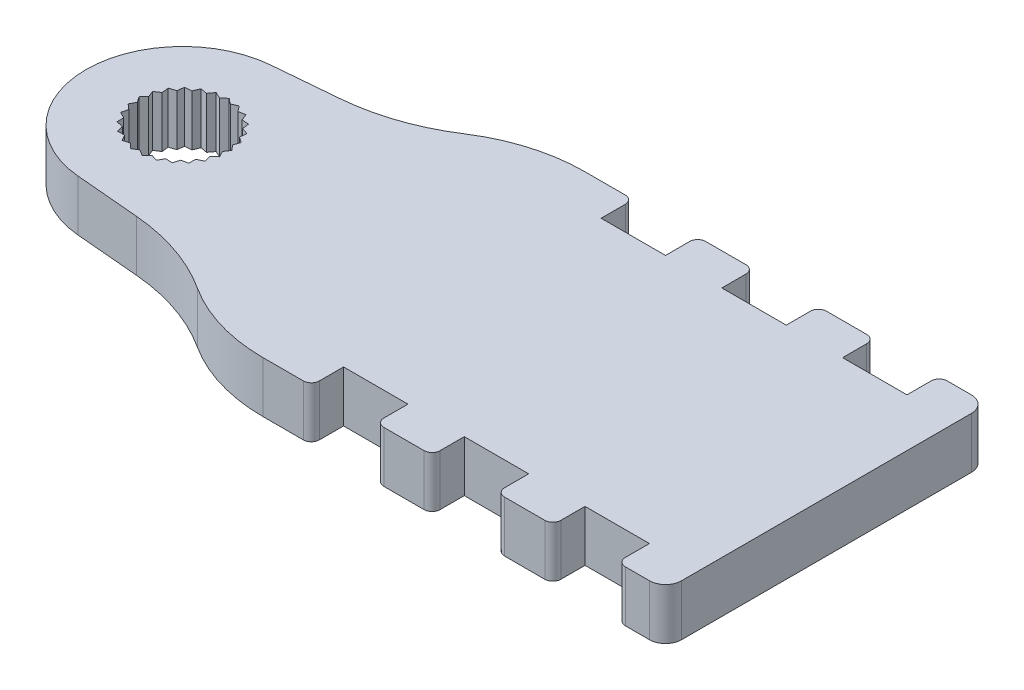
SolidWorks part; units mm, degrees
ref_plane "Front Plane" through (0, 0, 0) normal (0, 0, 1) x (1, 0, 0)
ref_plane "Top Plane" through (0, 0, 0) normal (0, 1, 0) x (1, 0, 0)
ref_plane "Right Plane" through (0, 0, 0) normal (1, 0, 0) x (0, 0, -1)
sketch "Sketch1" plane through (0, 0, 0) normal (0, 1, 0) x (1, 0, 0)
  line L0 (0, 2.895) -> (-0.3321, 2.6291)
  line L1 (0, 2.895) -> (0.3321, 2.6291)
  line L2 (0.72, 2.804) -> (0.3321, 2.6291)
  line L3 (0.72, 2.804) -> (0.9755, 2.4639)
  line L4 (1.3947, 2.5369) -> (0.9755, 2.4639)
  line L5 (1.3947, 2.5369) -> (1.5576, 2.1439)
  line L6 (1.9818, 2.1104) -> (1.5576, 2.1439)
  line L7 (1.9818, 2.1104) -> (2.0419, 1.6892)
  line L8 (2.4443, 1.5512) -> (2.0419, 1.6892)
  line L9 (2.4443, 1.5512) -> (2.3978, 1.1283)
  line L10 (2.7533, 0.8946) -> (2.3978, 1.1283)
  line L11 (2.7533, 0.8946) -> (2.6031, 0.4966)
  line L12 (2.8893, 0.1818) -> (2.6031, 0.4966)
  line L13 (2.8893, 0.1818) -> (2.6448, -0.1664)
  line L14 (2.8437, -0.5425) -> (2.6448, -0.1664)
  line L15 (2.8437, -0.5425) -> (2.5203, -0.8189)
  line L16 (2.6195, -1.2326) -> (2.5203, -0.8189)
  line L17 (2.6195, -1.2326) -> (2.2375, -1.4199)
  line L18 (2.2306, -1.8453) -> (2.2375, -1.4199)
  line L19 (2.2306, -1.8453) -> (1.814, -1.9318)
  line L20 (1.7016, -2.3421) -> (1.814, -1.9318)
  line L21 (1.7016, -2.3421) -> (1.2766, -2.3222)
  line L22 (1.0657, -2.6917) -> (1.2766, -2.3222)
  line L23 (1.0657, -2.6917) -> (0.659, -2.5667)
  line L24 (0.3628, -2.8722) -> (0.659, -2.5667)
  line L25 (0.3628, -2.8722) -> (0, -2.65)
  line L26 (-0.3628, -2.8722) -> (0, -2.65)
  line L27 (-0.3628, -2.8722) -> (-0.659, -2.5667)
  line L28 (-1.0657, -2.6917) -> (-0.659, -2.5667)
  line L29 (-1.0657, -2.6917) -> (-1.2766, -2.3222)
  line L30 (-1.7016, -2.3421) -> (-1.2766, -2.3222)
  line L31 (-1.7016, -2.3421) -> (-1.814, -1.9318)
  line L32 (-2.2306, -1.8453) -> (-1.814, -1.9318)
  line L33 (-2.2306, -1.8453) -> (-2.2375, -1.4199)
  line L34 (-2.6195, -1.2326) -> (-2.2375, -1.4199)
  line L35 (-2.6195, -1.2326) -> (-2.5203, -0.8189)
  line L36 (-2.8437, -0.5425) -> (-2.5203, -0.8189)
  line L37 (-2.8437, -0.5425) -> (-2.6448, -0.1664)
  line L38 (-2.8893, 0.1818) -> (-2.6448, -0.1664)
  line L39 (-2.8893, 0.1818) -> (-2.6031, 0.4966)
  line L40 (-2.7533, 0.8946) -> (-2.6031, 0.4966)
  line L41 (-2.7533, 0.8946) -> (-2.3978, 1.1283)
  line L42 (-2.4443, 1.5512) -> (-2.3978, 1.1283)
  line L43 (-2.4443, 1.5512) -> (-2.0419, 1.6892)
  line L44 (-1.9818, 2.1104) -> (-2.0419, 1.6892)
  line L45 (-1.9818, 2.1104) -> (-1.5576, 2.1439)
  line L46 (-1.3947, 2.5369) -> (-1.5576, 2.1439)
  line L47 (-1.3947, 2.5369) -> (-0.9755, 2.4639)
  line L48 (-0.72, 2.804) -> (-0.9755, 2.4639)
  line L49 (-0.72, 2.804) -> (-0.3321, 2.6291)
  line L52 (0, 0) -> (40, 0) construction
  line L74 (40, -10) -> (40, 10)
  line L75 (40, 10) -> (37, 10)
  line L76 (40, -10) -> (37, -10)
  line L79 (3.4771, 6.3271) -> (-0.5229, 5.9772)
  line L81 (3.4771, -6.3271) -> (-0.5229, -5.9772)
  line L82 (37, 10) -> (37, 8)
  line L83 (37, 8) -> (33, 8)
  line L84 (33, 8) -> (33, 10)
  line L86 (25.5, 8) -> (25.5, 10)
  line L87 (29.5, 8) -> (25.5, 8)
  line L88 (29.5, 10) -> (29.5, 8)
  line L89 (18, 8) -> (18, 10)
  line L90 (22, 8) -> (18, 8)
  line L91 (22, 10) -> (22, 8)
  line L92 (33, 8) -> (25.5, 8) construction
  line L93 (18, 10) -> (15, 10)
  line L94 (25.5, 10) -> (22, 10)
  line L95 (33, 10) -> (29.5, 10)
  line L97 (22, -10) -> (22, -8)
  line L98 (22, -8) -> (18, -8)
  line L99 (18, -8) -> (18, -10)
  line L100 (29.5, -10) -> (29.5, -8)
  line L101 (29.5, -8) -> (25.5, -8)
  line L102 (25.5, -8) -> (25.5, -10)
  line L103 (33, -8) -> (33, -10)
  line L104 (37, -10) -> (37, -8)
  line L105 (37, -8) -> (33, -8)
  line L106 (18, -10) -> (15, -10)
  line L107 (25.5, -10) -> (22, -10)
  line L108 (33, -10) -> (29.5, -10)
  circle A0 centre (0, 0) radius 2.895 construction
  circle A1 centre (0, 0) radius 2.65 construction
  arc A4 (-0.5229, 5.9772) -> (-0.5229, -5.9772) centre (0, 0) ccw
  arc A5 (15, 10) -> (9.2096, 8.2928) centre (15, -0.6735) ccw
  arc A6 (9.2096, 8.2928) -> (3.4771, 6.3271) centre (2.3798, 18.8687) cw
  arc A7 (15, -10) -> (9.2096, -8.2928) centre (15, 0.6735) cw
  arc A8 (9.2096, -8.2928) -> (3.4771, -6.3271) centre (2.3798, -18.8687) ccw
  point P17 (40, 0)
  point P82 (0, 0)
  dimension "D1" = 5.79
  dimension "D2" = 5.3
  dimension "D4" = 12
  dimension "D5" = 40
  dimension "D6" = 20
  dimension "D7" = 25
  dimension "D9" = 4
  dimension "D8" = 5
  dimension "D10" = 2
  dimension "D11" = 4
  dimension "D12" = 3
  dimension "D13" = 7.5
  dimension "D3" = 25
extrude "Boss-Extrude1" add sketch "Sketch1" along normal blind 3.175
fillet "Fillet2" radius 1 2 edges at (40, 1.5875, 10) (40, 1.5875, -10)
fillet "Fillet3" radius 0.5 12 edges at (37, 1.5875, 10) (33, 1.5875, 10) (29.5, 1.5875, 10) (25.5, 1.5875, 10) (22, 1.5875, 10) (18, 1.5875, 10) (18, 1.5875, -10) (22, 1.5875, -10) (25.5, 1.5875, -10) (29.5, 1.5875, -10) (33, 1.5875, -10) (37, 1.5875, -10)
